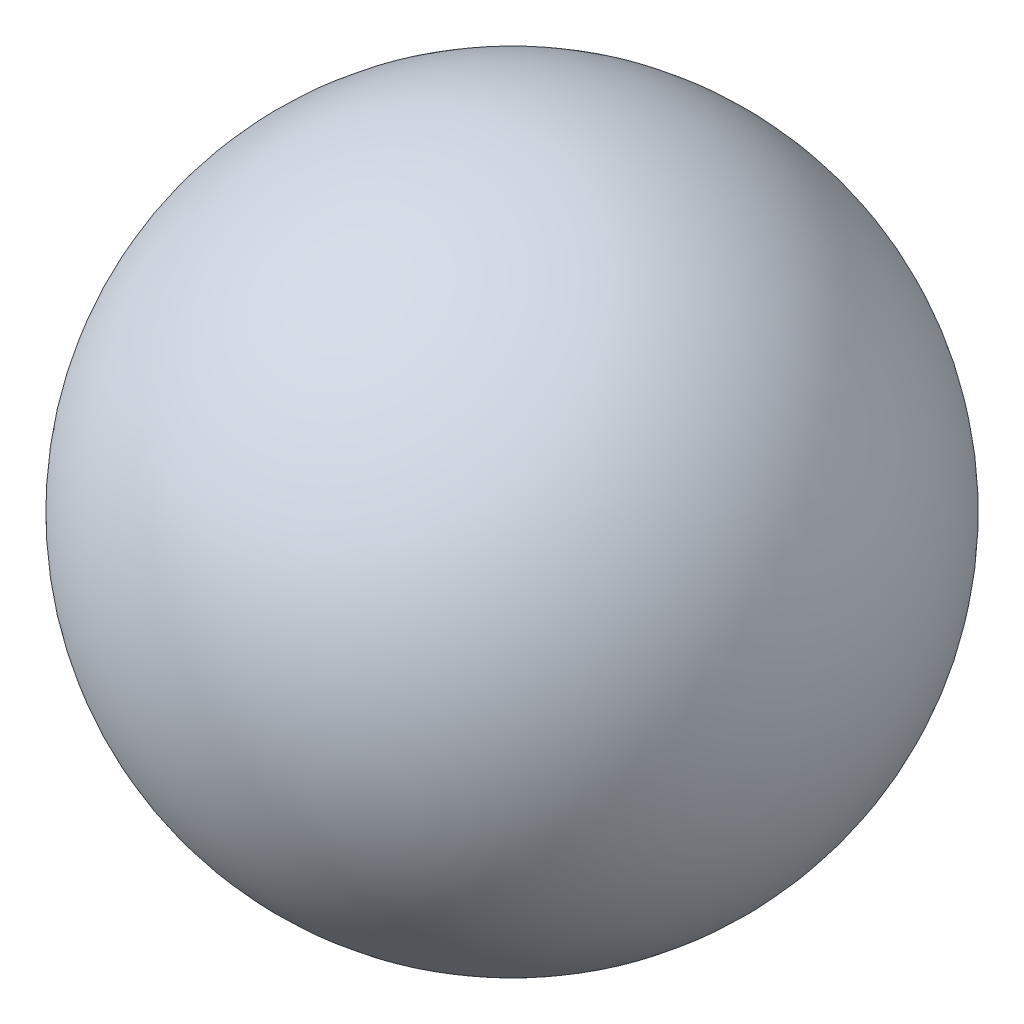
SolidWorks part; units mm, degrees
ref_plane "Front Plane" through (0, 0, 0) normal (0, 0, 1) x (1, 0, 0)
ref_plane "Top Plane" through (0, 0, 0) normal (0, 1, 0) x (1, 0, 0)
ref_plane "Right Plane" through (0, 0, 0) normal (1, 0, 0) x (0, 0, -1)
sketch "Sketch1" plane through (0, 0, 0) normal (0, 0, 1) x (1, 0, 0)
  line L0 (0, 60.7452) -> (0, -60.7452)
  arc A0 (0, 60.7452) -> (0, -60.7452) centre (0, 0) ccw
revolve "Revolve2" add sketch "Sketch1" angle 360 about L0
